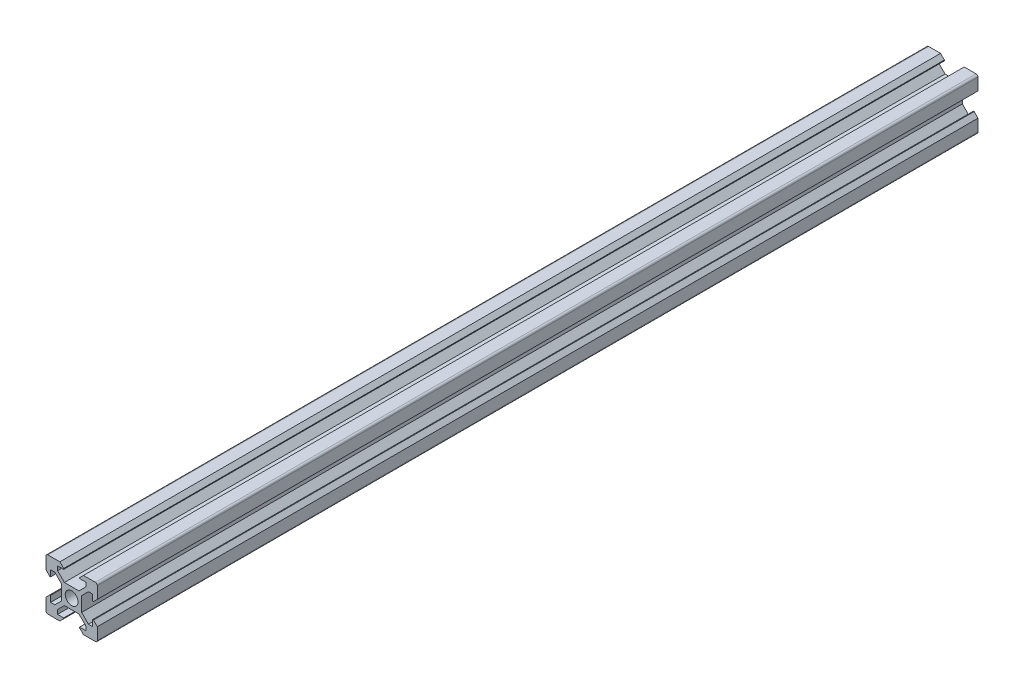
SolidWorks part; units mm, degrees
other "Markup1"
sketch "Sketch1" plane through (10, 10, 480) normal (0.5774, 0.5773, 0.5774) x (0.7071, 0, -0.7071)
ref_plane "Alzado" through (0, 0, 0) normal (0, 0, 1) x (1, 0, 0)
ref_plane "Planta" through (0, 0, 0) normal (0, 1, 0) x (1, 0, 0)
ref_plane "Vista lateral" through (0, 0, 0) normal (1, 0, 0) x (0, 0, -1)
sketch "Croquis1" plane through (0, 0, 0) normal (0, 0, 1) x (1, 0, 0)
  line L0 (-4.6, 10) -> (-3.1, 8.5)
  line L3 (-4.6, 10) -> (-9.25, 10)
  line L5 (-3.1, 8.5) -> (-3.1, 8.2)
  line L6 (-3.1, 8.2) -> (-5.5, 8.2)
  line L7 (-5.5, 8.2) -> (-5.5, 6.5607)
  line L8 (-5.5, 6.5607) -> (-2.84, 3.9007)
  line L9 (-2.84, 3.9007) -> (0, 3.9007)
  line L10 (0, 0) -> (-15.3499, 15.3499) construction
  line L11 (-3.9007, 2.84) -> (-3.9007, 0)
  line L12 (-6.5607, 5.5) -> (-3.9007, 2.84)
  line L13 (-8.2, 5.5) -> (-6.5607, 5.5)
  line L14 (-8.2, 3.1) -> (-8.2, 5.5)
  line L15 (-8.5, 3.1) -> (-8.2, 3.1)
  line L16 (-10, 4.6) -> (-10, 9.25)
  line L17 (-10, 4.6) -> (-8.5, 3.1)
  line L18 (10, 4.6) -> (8.5, 3.1)
  line L19 (10, 4.6) -> (10, 9.25)
  line L20 (8.5, 3.1) -> (8.2, 3.1)
  line L21 (8.2, 3.1) -> (8.2, 5.5)
  line L22 (8.2, 5.5) -> (6.5607, 5.5)
  line L23 (6.5607, 5.5) -> (3.9007, 2.84)
  line L24 (3.9007, 2.84) -> (3.9007, 0)
  line L25 (5.5, 6.5607) -> (2.84, 3.9007)
  line L26 (5.5, 8.2) -> (5.5, 6.5607)
  line L27 (3.1, 8.2) -> (5.5, 8.2)
  line L28 (3.1, 8.5) -> (3.1, 8.2)
  line L29 (4.6, 10) -> (9.25, 10)
  line L30 (4.6, 10) -> (3.1, 8.5)
  line L31 (2.84, 3.9007) -> (0, 3.9007)
  line L32 (4.6, -10) -> (3.1, -8.5)
  line L33 (4.6, -10) -> (9.25, -10)
  line L34 (3.1, -8.5) -> (3.1, -8.2)
  line L35 (3.1, -8.2) -> (5.5, -8.2)
  line L36 (5.5, -8.2) -> (5.5, -6.5607)
  line L37 (5.5, -6.5607) -> (2.84, -3.9007)
  line L38 (2.84, -3.9007) -> (0, -3.9007)
  line L39 (6.5607, -5.5) -> (3.9007, -2.84)
  line L40 (8.2, -5.5) -> (6.5607, -5.5)
  line L41 (8.2, -3.1) -> (8.2, -5.5)
  line L42 (8.5, -3.1) -> (8.2, -3.1)
  line L43 (10, -4.6) -> (10, -9.25)
  line L44 (10, -4.6) -> (8.5, -3.1)
  line L45 (3.9007, -2.84) -> (3.9007, 0)
  line L46 (-10, -4.6) -> (-8.5, -3.1)
  line L47 (-10, -4.6) -> (-10, -9.25)
  line L48 (-8.5, -3.1) -> (-8.2, -3.1)
  line L49 (-8.2, -3.1) -> (-8.2, -5.5)
  line L50 (-8.2, -5.5) -> (-6.5607, -5.5)
  line L51 (-6.5607, -5.5) -> (-3.9007, -2.84)
  line L52 (-3.9007, -2.84) -> (-3.9007, 0)
  line L53 (-5.5, -6.5607) -> (-2.84, -3.9007)
  line L54 (-5.5, -8.2) -> (-5.5, -6.5607)
  line L55 (-3.1, -8.2) -> (-5.5, -8.2)
  line L56 (-3.1, -8.5) -> (-3.1, -8.2)
  line L57 (-4.6, -10) -> (-9.25, -10)
  line L58 (-4.6, -10) -> (-3.1, -8.5)
  line L59 (-2.84, -3.9007) -> (0, -3.9007)
  circle A0 centre (0, 0) radius 2.5
  arc A1 (-9.25, 10) -> (-10, 9.25) centre (-9.25, 9.25) ccw
  arc A2 (10, 9.25) -> (9.25, 10) centre (9.25, 9.25) ccw
  arc A3 (9.25, -10) -> (10, -9.25) centre (9.25, -9.25) ccw
  arc A4 (-10, -9.25) -> (-9.25, -10) centre (-9.25, -9.25) ccw
  point P18 (-10, 10)
  point P37 (10, 10)
  point P55 (10, -10)
  point P73 (-10, -10)
  point P79 (0, 0)
  dimension "D1" = 5
  dimension "D5" = 0.75
  dimension "D2" = 10
  dimension "D3" = 10
  dimension "D4" = 4.6
  dimension "D6" = 5.5
  dimension "D7" = 135
  dimension "D8" = 0.75
  dimension "D9" = 225
  dimension "D10" = 2.84
  dimension "D11" = 1.8
  dimension "D12" = 3.1
  dimension "D13" = 4
extrude "Saliente-Extruir1" add sketch "Croquis1" along normal blind 343.37
